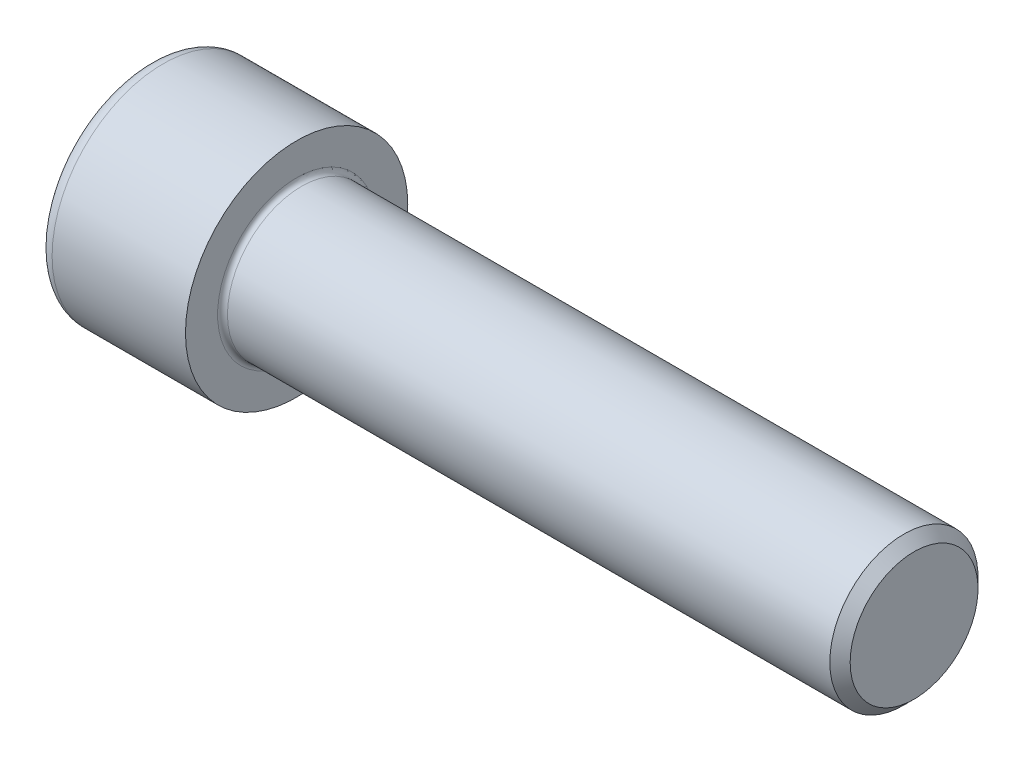
SolidWorks part; units mm, degrees
ref_plane "Front Plane" through (0, 0, 0) normal (0, 0, 1) x (1, 0, 0)
ref_plane "Top Plane" through (0, 0, 0) normal (0, 1, 0) x (1, 0, 0)
ref_plane "Right Plane" through (0, 0, 0) normal (1, 0, 0) x (0, 0, -1)
other "Configuration Table"
sketch "BaseHeadSke" plane through (0, 0, 0) normal (1, 0, 0) x (0, 0, -1)
  circle A1 centre (0, 0) radius 18
  dimension "Head_diameter" = 36
extrude "BaseHead" add sketch "BaseHeadSke" along normal blind 24
sketch "BodySke" plane through (0, 0, 0) normal (0, 0, 1) x (1, 0, 0)
  line L0 (0, 0) -> (124, 0)
  line L1 (124, 0) -> (124, 10.352)
  line L2 (124, 10.352) -> (122.352, 12)
  line L3 (122.352, 12) -> (0, 12)
  line L4 (0, 12) -> (0, 0)
  line L6 (0, 0) -> (159.3976, 0) construction
  line L7 (64, -84.3176) -> (64, 77.7215) construction
  line L8 (121, -21.5941) -> (121, 39.2994) construction
  line L10 (24, -18) -> (24, 18) construction
  dimension "Ang" = 45
  dimension "Thread_length" = 8
  dimension "Advance" = 0.5
revolve "BaseBody" add sketch "BodySke" angle 360 about L6
cosmetic thread "ThreadCosmetic" [suppressed] parameters "Thread_length"=8, "Thread_minor"=2.439
sketch "CutSocketSke" plane through (0, 0, 0) normal (1, 0, 0) x (0, 0, -1)
  line L1 (0, 10.9697) -> (-9.5, 5.4848)
  line L2 (-9.5, 5.4848) -> (-9.5, -5.4848)
  line L3 (-9.5, -5.4848) -> (0, -10.9697)
  line L4 (0, -10.9697) -> (9.5, -5.4848)
  line L5 (9.5, -5.4848) -> (9.5, 5.4848)
  line L6 (9.5, 5.4848) -> (0, 10.9697)
  circle A0 centre (0, 0) radius 9.5 construction
extrude "CutSocket" cut sketch "CutSocketSke" along normal blind 12
sketch "CutHoleSke" plane through (0, 0, 0) normal (0, 0, 1) x (1, 0, 0)
  line L0 (0, 0) -> (149.4323, 0) construction
  line L1 (0, 9.5) -> (13.6, 9.5)
  line L2 (13.6, 9.5) -> (19.0848, 0)
  line L3 (19.0848, 0) -> (0, 0)
  line L4 (0, 0) -> (0, 9.5)
  line L6 (24, -18) -> (24, 18) construction
  dimension "D1" = 60
  dimension "D2" = 2.5
revolve "CutHole" cut sketch "CutHoleSke" angle 360 about L0
fillet "Fillet1" radius 0.8 1 edges at (24, 0, -12)
fillet "Fillet2" radius 2.4 1 edges at (0, 0, -18)
sketch "ThdSchSke" plane through (0, 0, 0) normal (0, 0, 1) x (1, 0, 0)
  line L0 (120.0485, 13.9029) -> (120.0485, 12)
  line L1 (120.0485, 12) -> (121, 10.352)
  line L2 (121, 10.352) -> (121.9515, 12)
  line L3 (121.9515, 12) -> (121.9515, 13.9029)
  line L4 (121.9515, 13.9029) -> (120.0485, 13.9029)
  line L6 (0, 0) -> (141.9934, 0) construction
  line L7 (124, -10.352) -> (124, 10.352) construction
  dimension "D2" = 2.439
  dimension "D3" = 3
  dimension "Advance" = 0.5
revolve "ThreadSchematic" [suppressed] cut sketch "ThdSchSke" angle 360 about L6
pattern_linear "ThdSchPat" [suppressed] count 15 spacing 0.5 along (1, 0, 0)
equation "\"Thread_minor@ThreadCosmetic\" = \"Minor_dia@BodySke\""
equation "\"Thread_length@ThreadCosmetic\" = \"Thread_length@BodySke\""
equation "\"D2@CutHoleSke\" = \"Socket_width@CutSocketSke\""
equation "\"D2@ThdSchSke\" = \"Minor_dia@BodySke\""
equation "\"D3@ThdSchSke\" = \"Diameter@BodySke\""
equation "\"Advance@ThdSchSke\" = \"Advance@BodySke\""
equation "\"D3@ThdSchPat\" = \"Advance@BodySke\""
equation "\"D1@ThdSchPat\" =  int( \"Thread_length@BodySke\"/\"Advance@BodySke\" )-1"
